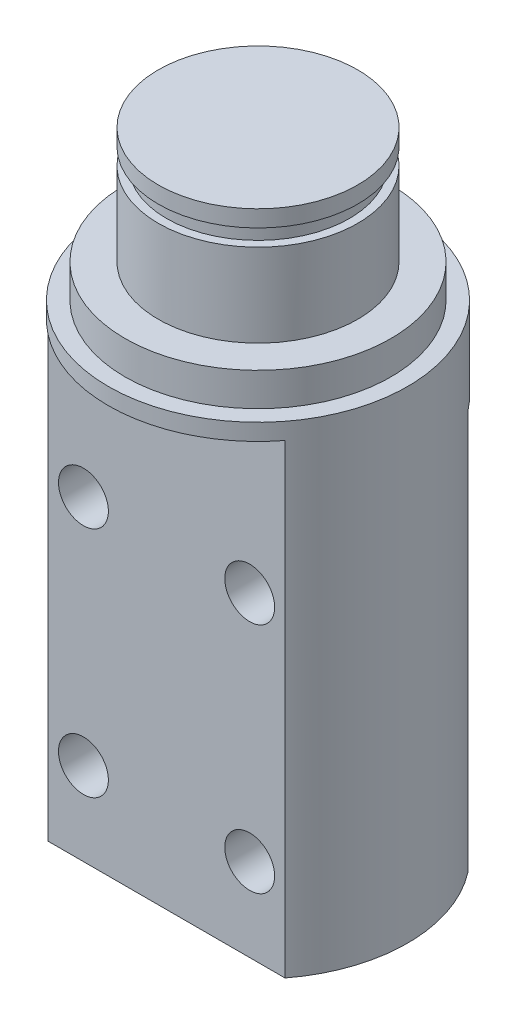
SolidWorks part; units mm, degrees
ref_plane "前视基准面" through (0, 0, 0) normal (0, 0, 1) x (1, 0, 0)
ref_plane "上视基准面" through (0, 0, 0) normal (0, 1, 0) x (1, 0, 0)
ref_plane "右视基准面" through (0, 0, 0) normal (1, 0, 0) x (0, 0, -1)
sketch "草图1" plane through (0, 0, 0) normal (0, 1, 0) x (1, 0, 0)
  circle A0 centre (0, 0) radius 6
  dimension "D1" = 12
extrude "凸台-拉伸1" add sketch "草图1" along normal blind 7
sketch "草图2" plane through (0, 0, 0) normal (0, -1, 0) x (1, 0, 0)
  circle A0 centre (0, 0) radius 9
  dimension "D1" = 18
extrude "凸台-拉伸2" add sketch "草图2" along normal blind 31
sketch "草图3" plane through (0, -31, 0) normal (0, -1, 0) x (1, 0, 0)
  line L1 (-8.7309, -5.5) -> (10.8825, -5.5)
  line L2 (-8.7309, -5.5) -> (-8.7309, -9)
  line L3 (-8.7309, -9) -> (10.8825, -9)
  line L4 (10.8825, -5.5) -> (10.8825, -9)
  circle A0 centre (0, 0) radius 9 construction
  dimension "D1" = 3.5
extrude "切除-拉伸1" cut sketch "草图3" against normal blind 24
sketch "草图4" plane through (0, -31, 0) normal (0, -1, 0) x (1, 0, 0)
  line L1 (-8.6374, 9) -> (11.3814, 9)
  line L2 (-8.6374, 9) -> (-8.6374, 5.5)
  line L3 (-8.6374, 5.5) -> (11.3814, 5.5)
  line L4 (11.3814, 9) -> (11.3814, 5.5)
  circle A0 centre (0, 0) radius 9 construction
  dimension "D1" = 3.5
extrude "切除-拉伸2" cut sketch "草图4" against normal blind 28
sketch "草图5" plane through (0, 0, -5.5) normal (0, 0, -1) x (-1, 0, 0)
  line L0 (-7.1239, -31) -> (7.1239, -31) construction
  line L1 (-7.1239, -7) -> (7.1239, -7) construction
  circle A0 centre (-5, -26) radius 1.5
  circle A1 centre (5, -26) radius 1.5
  circle A2 centre (5, -12) radius 1.5
  circle A3 centre (-5, -12) radius 1.5
  dimension "D1" = 3
  dimension "D2" = 3
  dimension "D5" = 10
  dimension "D6" = 5
  dimension "D8" = 3
  dimension "D9" = 3
  dimension "D3" = 5
  dimension "D4" = 5
  dimension "D7" = 10
  dimension "D10" = 5
extrude "切除-拉伸3" cut sketch "草图5" against normal blind 18
sketch "草图10" plane through (0, 7, 0) normal (0, 1, 0) x (1, 0, 0)
  circle A0 centre (0, 0) radius 2.9987
ref_plane "基准面1" through (0, 6, 0) normal (0, 1, 0) x (1, 0, 0)
sketch "草图11" plane through (0, 6, 0) normal (0, 1, 0) x (1, 0, 0)
  circle A0 centre (0, 0) radius 5.5
  circle A1 centre (0, 0) radius 10.6382
  dimension "D1" = 11
extrude "切除-拉伸4" cut sketch "草图11" against normal blind 1
sketch "草图12" plane through (0, 0, 0) normal (0, 1, 0) x (1, 0, 0)
  circle A0 centre (0, 0) radius 8
  circle A1 centre (0, 0) radius 9
  dimension "D1" = 16
  dimension "D2" = 18
extrude "切除-拉伸7" cut sketch "草图12" against normal blind 2
